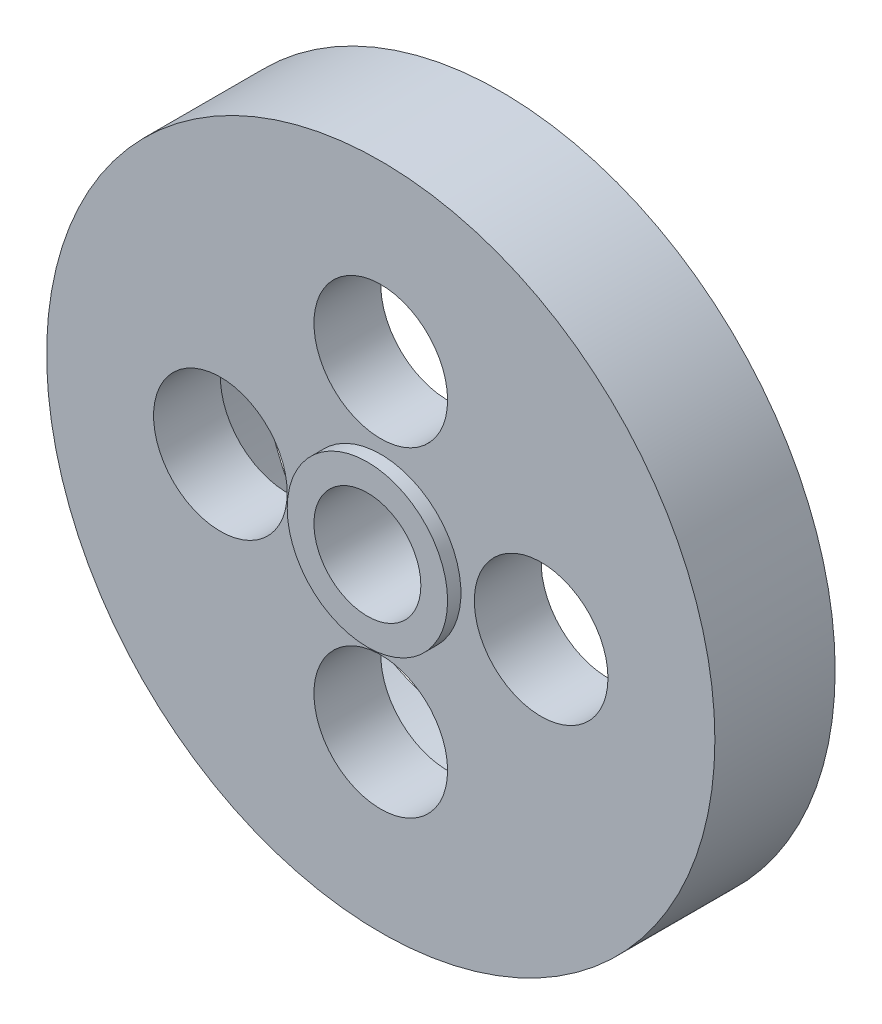
SolidWorks part; units mm, degrees
ref_plane "Front Plane" through (0, 0, 0) normal (0, 0, 1) x (1, 0, 0)
ref_plane "Top Plane" through (0, 0, 0) normal (0, 1, 0) x (1, 0, 0)
ref_plane "Right Plane" through (0, 0, 0) normal (1, 0, 0) x (0, 0, -1)
sketch "Эскиз1" plane through (0, 0, 0) normal (1, 0, 0) x (0, 0, -1)
  line L0 (0, 0) -> (28.0985, 0) construction
  line L1 (7.7391, 4) -> (7.7391, 25)
  line L2 (7.7391, 25) -> (16.7391, 25)
  line L3 (16.7391, 25) -> (16.7391, 18)
  line L4 (16.7391, 18) -> (12.7391, 18)
  line L5 (12.7391, 18) -> (12.7391, 4)
  line L6 (12.7391, 4) -> (7.7391, 4)
  point P9 (10.2391, 4)
  dimension "D1" = 4
  dimension "D2" = 21
  dimension "D3" = 14
  dimension "D4" = 4
  dimension "D5" = 9
revolve "Повернуть1" add sketch "Эскиз1" angle 360 about L0
sketch "Эскиз2" plane through (0, 0, -7.7391) normal (0, 0, 1) x (1, 0, 0)
  line L0 (-20.4331, 0) -> (19.9092, 0) construction
  line L1 (0, 19.9092) -> (0, -19.8044) construction
  circle A0 centre (0, 12) radius 5
  circle A1 centre (12, 0) radius 5
  circle A2 centre (0, -12) radius 5
  circle A3 centre (-12, 0) radius 5
  point P12 (0, 0)
  dimension "D1" = 10
  dimension "D2" = 12
  dimension "D3" = 4
extrude "Вырез-Вытянуть1" cut sketch "Эскиз2" against normal through all
sketch "Эскиз3" plane through (0, 0, -7.7391) normal (0, 0, 1) x (1, 0, 0)
  circle A0 centre (0, 0) radius 4
  circle A1 centre (0, 0) radius 6
  dimension "D1" = 8
  dimension "D2" = 12
extrude "Бобышка-Вытянуть1" add sketch "Эскиз3" along normal blind 1
